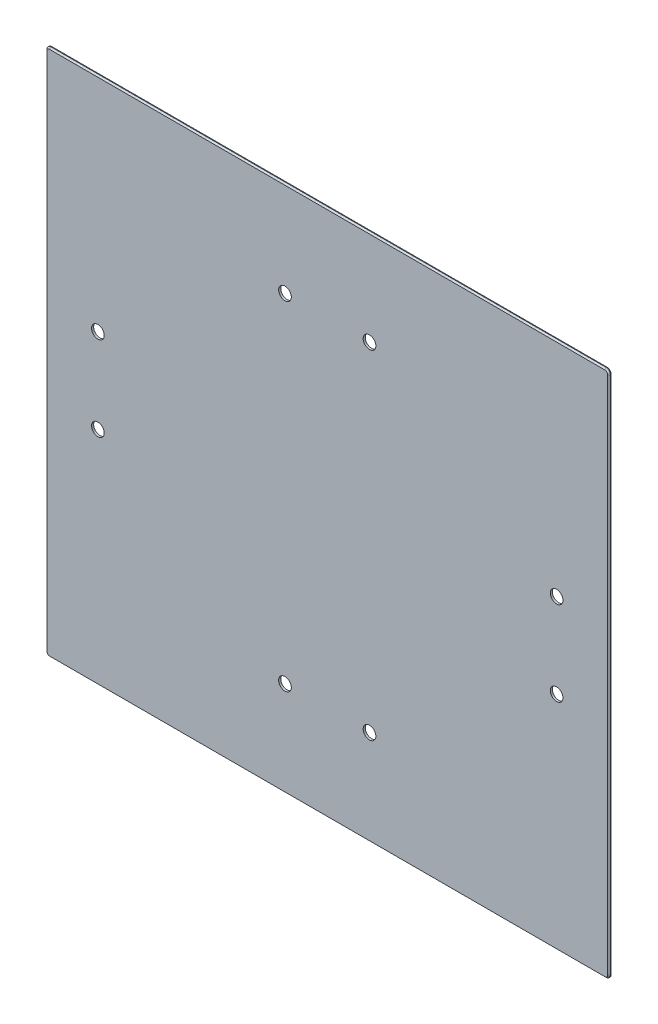
SolidWorks part; units mm, degrees
material "Plain Carbon Steel"
ref_plane "Front Plane" through (0, 0, 0) normal (0, 0, 1) x (1, 0, 0)
ref_plane "Top Plane" through (0, 0, 0) normal (0, 1, 0) x (1, 0, 0)
ref_plane "Right Plane" through (0, 0, 0) normal (1, 0, 0) x (0, 0, -1)
sketch "Sketch1" plane through (0, 0, 0) normal (0, 0, 1) x (1, 0, 0)
  line L1 (-200, -187.5) -> (200, -187.5)
  line L2 (-200, -187.5) -> (-200, 187.5)
  line L3 (-200, 187.5) -> (200, 187.5)
  line L4 (200, -187.5) -> (200, 187.5)
  line L5 (-200, -187.5) -> (200, 187.5) construction
  line L6 (-200, 187.5) -> (200, -187.5) construction
  line L11 (-150, -140.625) -> (150, 140.625) construction
  line L12 (-150, 140.625) -> (150, -140.625) construction
  point P0 (0, 0)
  point P6 (0, 0)
  dimension "D2" = 400
  dimension "D3" = 375
extrude "Boss-Extrude1" add sketch "Sketch1" along normal blind 1.5 contours L2 L3 L4 L1
fillet "Fillet1" radius 3 4 edges at (-200, -187.5, 0.75) (200, -187.5, 0.75) (200, 187.5, 0.75) (-200, 187.5, 0.75)
chamfer "Chamfer1" distance 1 angle 45 8 edges at (-199.1213, 186.6213, 1.5) (0, 187.5, 1.5) (199.1213, 186.6213, 1.5) (200, 0, 1.5) (199.1213, -186.6213, 1.5) (0, -187.5, 1.5) (-199.1213, -186.6213, 1.5) (-200, 0, 1.5)
sketch "Sketch5" plane through (0, 0, 1.5) normal (0, 0, 1) x (1, 0, 0)
  line L0 (177.8, -127.9628) -> (177.8, 127.9628)
  line L1 (154.1116, 152.4) -> (-154.1116, 152.4)
  line L2 (-177.8, 127.9628) -> (-177.8, -127.9628)
  line L3 (-154.1116, -152.4) -> (154.1116, -152.4)
  line L4 (0, 152.4) -> (0, -152.4) construction
  line L5 (-177.8, 0) -> (177.8, 0) construction
  ellipse E0 centre (151.2816, -125.0434) end of major axis (168.3205, -147.7618) minor radius 25.4 (154.1116, -152.4) -> (177.8, -127.9628) ccw
  ellipse E1 centre (151.2816, 125.0434) end of major axis (168.3205, 147.7618) minor radius 25.4 (177.8, 127.9628) -> (154.1116, 152.4) ccw
  ellipse E2 centre (-151.2816, 125.0434) end of major axis (-168.3205, 147.7618) minor radius 25.4 (-154.1116, 152.4) -> (-177.8, 127.9628) ccw
  ellipse E3 centre (-151.2816, -125.0434) end of major axis (-168.3205, -147.7618) minor radius 25.4 (-177.8, -127.9628) -> (-154.1116, -152.4) ccw
sketch "Sketch6" plane through (0, 0, 1.5) normal (0, 0, 1) x (1, 0, 0)
  line L5 (-177.8, -127.9628) -> (-177.8, 127.9628)
  line L6 (-154.1116, 152.4) -> (154.1116, 152.4)
  line L7 (154.1116, -152.4) -> (-154.1116, -152.4)
  line L8 (177.8, 127.9628) -> (177.8, -127.9628)
  line L9 (0, 152.4) -> (0, -152.4) construction
  line L10 (-177.8, 0) -> (177.8, 0) construction
  circle A0 centre (-30, 120) radius 4.5
  circle A1 centre (30, 120) radius 4.5
  circle A2 centre (162.8, 30) radius 4.5
  circle A3 centre (162.8, -30) radius 4.5
  circle A4 centre (30, -120) radius 4.5
  circle A5 centre (-30, -120) radius 4.5
  circle A6 centre (-162.8, 30) radius 4.5
  circle A7 centre (-162.8, -30) radius 4.5
  dimension "D5" = 32.4
  dimension "D6" = 30
  dimension "D7" = 30
  dimension "D8" = 60
  dimension "D12" = 15
  dimension "D13" = 15
  dimension "D14" = 325.6
  dimension "D15" = 240
  dimension "D9" = 30
  dimension "D17" = 60
  dimension "D18" = 60
  dimension "D19" = 30
  dimension "D20" = 9
  dimension "D21" = 9
  dimension "D22" = 9
  dimension "D23" = 9
  dimension "D24" = 9
  dimension "D25" = 9
  dimension "D26" = 9
  dimension "D27" = 9
  dimension "D2" = 15
  dimension "D3" = 30
  dimension "D4" = 32.4
  dimension "D10" = 30
  dimension "D11" = 30
  dimension "D16" = 30
extrude "Cut-Extrude1" cut sketch "Sketch6" against normal blind 10 contours A0 | A6 | A7 | A5 | A4 | A3 | A2 | A1
